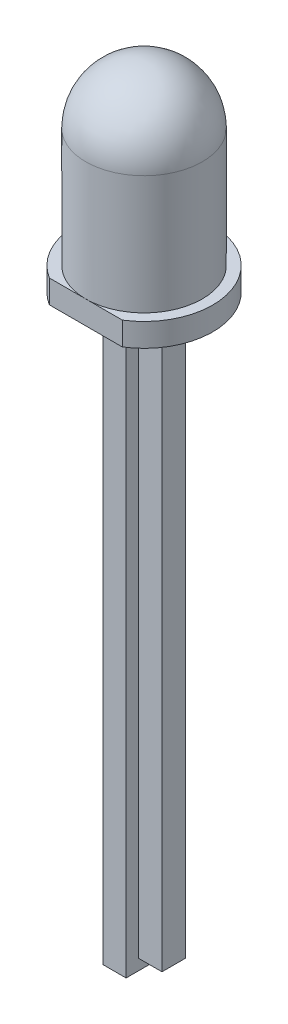
SolidWorks part; units mm, degrees
ref_plane "Front Plane" through (0, 0, 0) normal (0, 0, 1) x (1, 0, 0)
ref_plane "Top Plane" through (0, 0, 0) normal (0, 1, 0) x (1, 0, 0)
ref_plane "Right Plane" through (0, 0, 0) normal (1, 0, 0) x (0, 0, -1)
sketch "Sketch1" plane through (0, 0, 0) normal (0, 1, 0) x (1, 0, 0)
  line L5 (-0.5, 0.5) -> (2.04, 0.5)
  line L6 (-0.5, 0.5) -> (-0.5, -0.5)
  line L7 (-0.5, -0.5) -> (2.04, -0.5)
  line L8 (2.04, 0.5) -> (2.04, -0.5)
  dimension "D1" = 0.5
  dimension "D2" = 0.5
  dimension "D3" = 2.54
  dimension "D4" = 0.5
extrude "Base-Extrude" add sketch "Sketch1" along normal blind 0.381
sketch "Sketch2" plane through (0, 0, 0) normal (0, -1, 0) x (1, 0, 0)
  line L0 (2.04, -0.5) -> (-0.5, -0.5) construction
  line L1 (-0.5, 0.5) -> (0.5, 0.5)
  line L2 (-0.5, 0.5) -> (-0.5, -0.5)
  line L3 (-0.5, -0.5) -> (0.5, -0.5)
  line L4 (0.5, 0.5) -> (0.5, -0.5)
  line L6 (2.04, 0.5) -> (1.04, 0.5)
  line L7 (2.04, 0.5) -> (2.04, -0.5)
  line L8 (2.04, -0.5) -> (1.04, -0.5)
  line L9 (1.04, 0.5) -> (1.04, -0.5)
extrude "Boss-Extrude1" add sketch "Sketch2" along normal blind 24
sketch "Sketch7" plane through (0, -24, 0) normal (0, -1, 0) x (1, 0, 0)
  line L4 (-0.5, 0.5) -> (-0.5, -0.5)
  line L5 (-0.5, -0.5) -> (0.5, -0.5)
  line L6 (0.5, -0.5) -> (0.5, 0.5)
  line L7 (0.5, 0.5) -> (-0.5, 0.5)
  line L8 (-0.5, 0.5) -> (-0.5, -0.5)
  line L9 (-0.5, -0.5) -> (0.5, -0.5)
  line L10 (0.5, -0.5) -> (0.5, 0.5)
  line L11 (0.5, 0.5) -> (-0.5, 0.5)
  dimension "D1" = 0
extrude "Boss-Extrude4" add sketch "Sketch7" along normal blind 1
fillet "Fillet5" radius 0.254 6 edges at (2.04, 0.381, 0) (1.04, 0, 0) (-0.5, 0.381, 0)
sketch "Sketch3" plane through (0, 0.381, 0) normal (0, 1, 0) x (-1, 0, 0)
  line L0 (-0.77, 0) -> (-0.77, 0.5) construction
  line L1 (0.246, 0.5) -> (-1.786, 0.5) construction
  line L2 (-0.77, 0) -> (-2.04, 0) construction
  line L3 (-2.04, 0.5) -> (-2.04, -0.5) construction
  line L4 (-2.336, 2.5) -> (0.796, 2.5)
  arc A0 (-2.336, 2.5) -> (0.796, 2.5) centre (-0.77, 0) ccw
  circle A1 centre (-0.77, 0) radius 2.5 construction
  dimension "D1" = 5.9
  dimension "D2" = 5
extrude "Boss-Extrude2" add sketch "Sketch3" along normal blind 1
sketch "Sketch4" plane through (0, 1.381, 0) normal (0, 1, 0) x (-1, 0, 0)
  line L0 (0.796, 2.5) -> (-2.336, 2.5) construction
  circle A0 centre (-0.77, 0) radius 2.5
extrude "Boss-Extrude3" add sketch "Sketch4" along normal blind 7.6
fillet "Fillet4" radius 2.5 1 edges at (0.77, 8.981, 2.5)
sketch "Sketch6" plane through (0, 0, 0.5) normal (0, 0, 1) x (1, 0, 0)
  line L0 (-0.246, 0.381) -> (1.786, 0.381) construction
  line L1 (0.754, 0.381) -> (0.786, 0.381)
  line L2 (0.754, 0.381) -> (0.754, 0)
  line L3 (0.754, 0) -> (0.786, 0)
  line L4 (0.786, 0.381) -> (0.786, 0)
extrude "Cut-Extrude1" cut sketch "Sketch6" against normal through all
sketch "Component_Outline" plane through (0, 0, 0) normal (0, 1, 0) x (1, 0, 0)
  line L0 (-0.796, -2.5) -> (2.336, -2.5)
  arc A0 (2.336, -2.5) -> (-0.796, -2.5) centre (0.77, 0) ccw
  arc A1 (2.336, -2.5) -> (-0.796, -2.5) centre (0.77, 0) ccw construction
